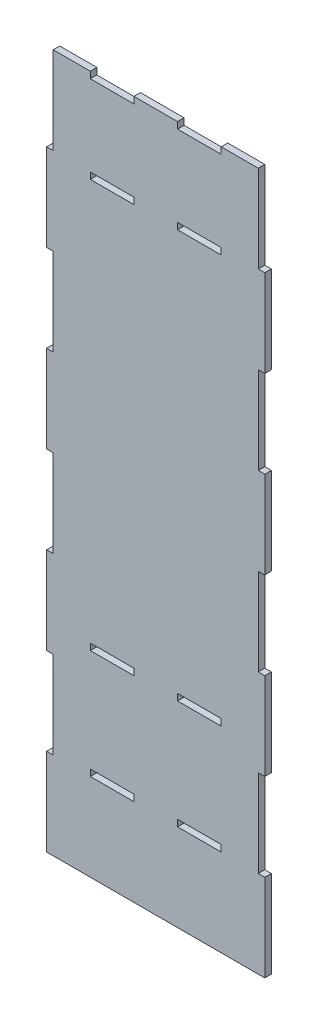
SolidWorks part; units mm, degrees
material "玻璃"
ref_plane "前视基准面" through (0, 0, 0) normal (0, 0, 1) x (1, 0, 0)
ref_plane "上视基准面" through (0, 0, 0) normal (0, 1, 0) x (1, 0, 0)
ref_plane "右视基准面" through (0, 0, 0) normal (1, 0, 0) x (0, 0, -1)
sketch "草图1" plane through (0, 0, 0) normal (0, 0, 1) x (1, 0, 0)
  line L0 (-148.3444, 0) -> (124.5033, 0) construction
  line L1 (0, 306.377) -> (0, -104.9007) construction
  line L7 (50, -50.596) -> (50, -10.596)
  line L8 (50, -10.596) -> (47, -10.596)
  line L9 (47, -10.596) -> (47, 29.404)
  line L10 (47, 29.404) -> (50, 29.404)
  line L11 (50, 29.404) -> (50, 69.404)
  line L12 (50, 69.404) -> (47, 69.404)
  line L13 (47, 69.404) -> (47, 109.404)
  line L14 (47, 109.404) -> (50, 109.404)
  line L15 (50, 109.404) -> (50, 149.404)
  line L16 (50, 149.404) -> (47, 149.404)
  line L17 (47, 149.404) -> (47, 189.404)
  line L18 (47, 189.404) -> (50, 189.404)
  line L19 (50, 189.404) -> (50, 229.404)
  line L20 (50, 229.404) -> (47, 229.404)
  line L21 (47, 229.404) -> (47, 269.404)
  line L23 (30, 269.404) -> (30, 266.404)
  line L25 (10, 266.404) -> (10, 269.404)
  line L27 (148.3444, 0) -> (-124.5033, 0) construction
  line L28 (-10, 266.404) -> (-10, 269.404)
  line L30 (-30, 269.404) -> (-30, 266.404)
  line L31 (-47, 269.404) -> (-30, 269.404)
  line L32 (-47, 229.404) -> (-47, 269.404)
  line L33 (-50, 229.404) -> (-47, 229.404)
  line L34 (-50, 189.404) -> (-50, 229.404)
  line L35 (-47, 189.404) -> (-50, 189.404)
  line L36 (-47, 149.404) -> (-47, 189.404)
  line L37 (-50, 149.404) -> (-47, 149.404)
  line L38 (-50, 109.404) -> (-50, 149.404)
  line L39 (-47, 109.404) -> (-50, 109.404)
  line L40 (-47, 69.404) -> (-47, 109.404)
  line L41 (-50, 69.404) -> (-47, 69.404)
  line L42 (-50, 29.404) -> (-50, 69.404)
  line L43 (-47, 29.404) -> (-50, 29.404)
  line L44 (-47, -10.596) -> (-47, 29.404)
  line L45 (-50, -10.596) -> (-47, -10.596)
  line L46 (-50, -50.596) -> (-50, -10.596)
  line L59 (-30, 266.404) -> (-10, 266.404)
  line L60 (-10, 269.404) -> (10, 269.404)
  line L61 (10, 266.404) -> (30, 266.404)
  line L62 (30, 269.404) -> (47, 269.404)
  line L80 (-50, -50.596) -> (50, -50.596)
  line L81 (-30, 42.404) -> (-10, 42.404)
  line L82 (-10, 42.404) -> (-10, 39.404)
  line L83 (-10, 39.404) -> (-30, 39.404)
  line L84 (-30, 39.404) -> (-30, 42.404)
  line L85 (-30, -7.596) -> (-10, -7.596)
  line L86 (-10, -7.596) -> (-10, -10.596)
  line L87 (-10, -10.596) -> (-30, -10.596)
  line L88 (-30, -10.596) -> (-30, -7.596)
  line L89 (10, 42.404) -> (10, 39.404)
  line L90 (30, 39.404) -> (30, 42.404)
  line L91 (30, 42.404) -> (10, 42.404)
  line L92 (10, 39.404) -> (30, 39.404)
  line L93 (10, -7.596) -> (10, -10.596)
  line L94 (30, -7.596) -> (10, -7.596)
  line L95 (10, -10.596) -> (30, -10.596)
  line L96 (30, -10.596) -> (30, -7.596)
  line L97 (-30, 229.404) -> (-10, 229.404)
  line L98 (-10, 229.404) -> (-10, 226.4452)
  line L99 (-10, 226.4452) -> (-30, 226.4452)
  line L100 (-30, 226.4452) -> (-30, 229.404)
  line L101 (10, 229.404) -> (10, 226.4452)
  line L102 (10, 226.4452) -> (30, 226.4452)
  line L103 (30, 229.404) -> (10, 229.404)
  line L104 (30, 226.4452) -> (30, 229.404)
  point P35 (0, 269.404)
  point P58 (0, -50.596)
  dimension "D1" = 3
  dimension "D2" = 3
  dimension "D3" = 40
  dimension "D4" = 20
  dimension "D5" = 20
  dimension "D6" = 17
  dimension "D7" = 3
  dimension "D8" = 3
  dimension "D9" = 90
extrude "凸台-拉伸1" add sketch "草图1" along normal blind 3
